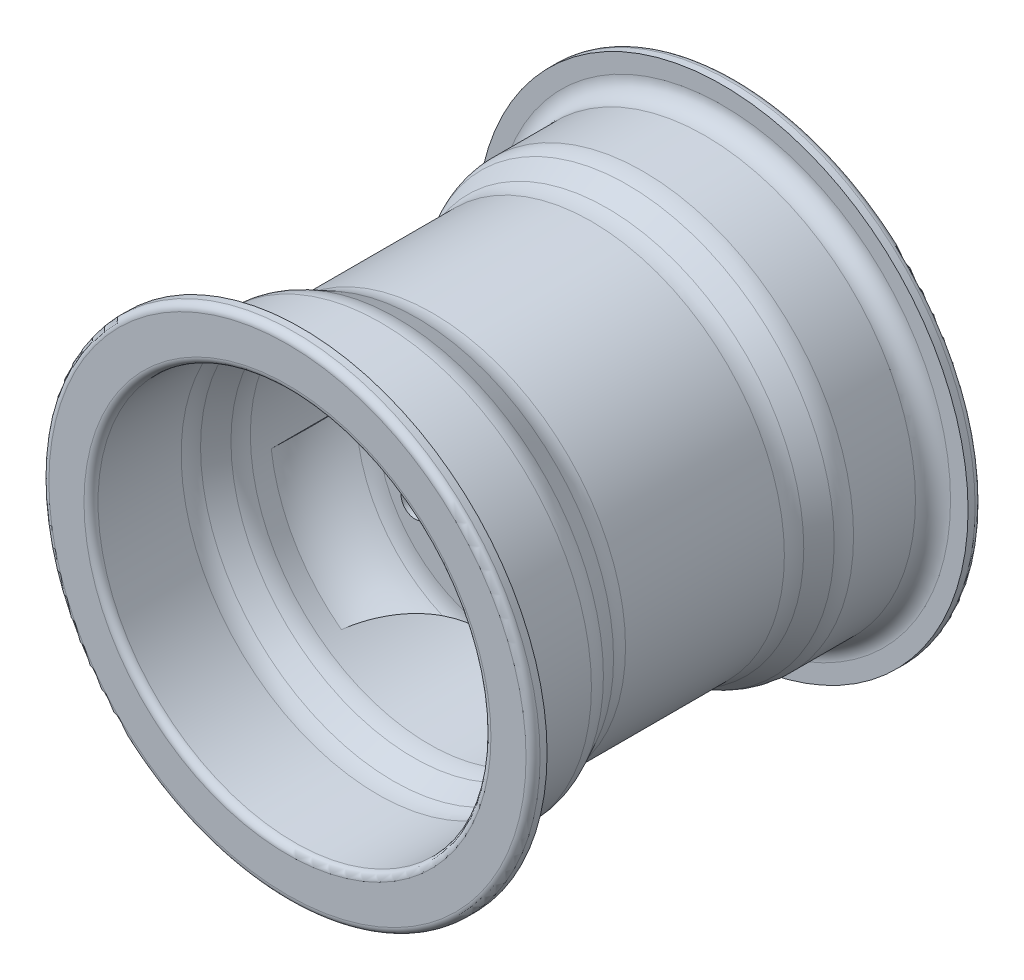
SolidWorks part; units mm, degrees
ref_plane "Front Plane" through (0, 0, 0) normal (0, 0, 1) x (1, 0, 0)
ref_plane "Top Plane" through (0, 0, 0) normal (0, 1, 0) x (1, 0, 0)
ref_plane "Right Plane" through (0, 0, 0) normal (1, 0, 0) x (0, 0, -1)
sketch "Sketch1" plane through (0, 0, 0) normal (1, 0, 0) x (0, 0, -1)
  line L0 (-51.3612, 0) -> (55.3802, 0) construction
  line L1 (0, 0) -> (0, 55) construction
  line L2 (-60, 70) -> (-60, 65)
  line L3 (-55, 60) -> (-37.3607, 60)
  line L4 (-32.8885, 58.9443) -> (-27.1115, 56.0557)
  line L5 (-22.6393, 55) -> (22.6393, 55)
  line L6 (-64, 68) -> (-64, 58)
  line L7 (-62, 56) -> (-38.305, 56)
  line L8 (-33.8328, 54.9443) -> (-28.0557, 52.0557)
  line L9 (-23.5836, 51) -> (-18, 51)
  line L10 (2.5, 20) -> (-2.5, 20)
  line L11 (-2.5, 20) -> (-2.5, 35.9602)
  line L12 (-25.9443, 51) -> (0, 51) construction
  line L13 (-62, 70) -> (-60, 70)
  line L14 (-64, 70) -> (-64, 56) construction
  line L15 (-64, 56) -> (-35.9443, 56) construction
  line L16 (-60, 70) -> (-60, 60) construction
  line L17 (-60, 60) -> (-35, 60) construction
  line L18 (-35, 60) -> (-25, 55) construction
  line L19 (-35.9443, 56) -> (-25.9443, 51) construction
  line L20 (-25, 55) -> (0, 55) construction
  line L21 (62, 70) -> (60, 70)
  line L22 (2.5, 20) -> (2.5, 35.9602)
  line L23 (23.5836, 51) -> (18, 51)
  line L24 (33.8328, 54.9443) -> (28.0557, 52.0557)
  line L25 (62, 56) -> (38.305, 56)
  line L26 (64, 68) -> (64, 58)
  line L27 (32.8885, 58.9443) -> (27.1115, 56.0557)
  line L28 (55, 60) -> (37.3607, 60)
  line L29 (60, 70) -> (60, 65)
  arc A0 (-3.6626, 40.64) -> (-18, 51) centre (-21.3374, 31.2804) ccw
  arc A1 (-64, 68) -> (-62, 70) centre (-62, 68) cw
  arc A2 (-64, 58) -> (-62, 56) centre (-62, 58) ccw
  arc A3 (-60, 65) -> (-55, 60) centre (-55, 65) ccw
  arc A4 (-37.3607, 60) -> (-32.8885, 58.9443) centre (-37.3607, 50) cw
  arc A5 (-28.0557, 52.0557) -> (-23.5836, 51) centre (-23.5836, 61) ccw
  arc A6 (-27.1115, 56.0557) -> (-22.6393, 55) centre (-22.6393, 65) ccw
  arc A7 (-38.305, 56) -> (-33.8328, 54.9443) centre (-38.305, 46) cw
  arc A8 (-2.5, 35.9602) -> (-3.6626, 40.64) centre (-12.5, 35.9602) ccw
  arc A9 (2.5, 35.9602) -> (3.6626, 40.64) centre (12.5, 35.9602) cw
  arc A10 (38.305, 56) -> (33.8328, 54.9443) centre (38.305, 46) ccw
  arc A11 (27.1115, 56.0557) -> (22.6393, 55) centre (22.6393, 65) cw
  arc A12 (28.0557, 52.0557) -> (23.5836, 51) centre (23.5836, 61) cw
  arc A13 (37.3607, 60) -> (32.8885, 58.9443) centre (37.3607, 50) ccw
  arc A14 (60, 65) -> (55, 60) centre (55, 65) cw
  arc A15 (64, 58) -> (62, 56) centre (62, 58) cw
  arc A16 (64, 68) -> (62, 70) centre (62, 68) ccw
  arc A17 (3.6626, 40.64) -> (18, 51) centre (21.3374, 31.2804) cw
  point P28 (-60, 60)
  point P43 (-2.5, 38)
  point P72 (0, 20)
  dimension "D12" = 20
  dimension "D11" = 2
  dimension "D13" = 5
  dimension "D14" = 10
  dimension "D2" = 10
  dimension "D3" = 10
  dimension "D1" = 55
  dimension "D4" = 60
  dimension "D5" = 10
  dimension "D6" = 70
  dimension "D8" = 20
  dimension "D9" = 18
  dimension "D10" = 2.5
  dimension "D7" = 4
revolve "Revolve1" add sketch "Sketch1" angle 360 about L0
sketch "Sketch2" plane through (0, 0, 0) normal (0, 0, 1) x (1, 0, 0)
  line L0 (0, 0) -> (0, 83.1982) construction
  line L1 (0, 0) -> (-97.9458, 0) construction
  line L2 (0, 0) -> (-76.9833, -44.4463) construction
  circle A0 centre (0, 0) radius 51 construction
  arc A1 (-20, 46.9148) -> (-50.6294, -6.1369) centre (0, 0) ccw
  arc A2 (-20, 46.9148) -> (-50.6294, -6.1369) centre (-117.7069, 67.9581) cw
  circle A3 centre (0, 29) radius 4
  arc A4 (50.6294, -6.1369) -> (20, 46.9148) centre (117.7069, 67.9581) cw
  arc A5 (50.6294, -6.1369) -> (20, 46.9148) centre (0, 0) ccw
  circle A6 centre (25.1147, -14.5) radius 4
  arc A7 (-30.6294, -40.7779) -> (30.6294, -40.7779) centre (0, -135.9163) cw
  arc A8 (-30.6294, -40.7779) -> (30.6294, -40.7779) centre (0, 0) ccw
  circle A9 centre (-25.1147, -14.5) radius 4
  dimension "D4" = 8
  dimension "D1" = 30
  dimension "D2" = 20
  dimension "D3" = 20
  dimension "D5" = 29
  dimension "D6" = 3
extrude "Cut-Extrude1" cut sketch "Sketch2" against normal through all both and the other way through all
